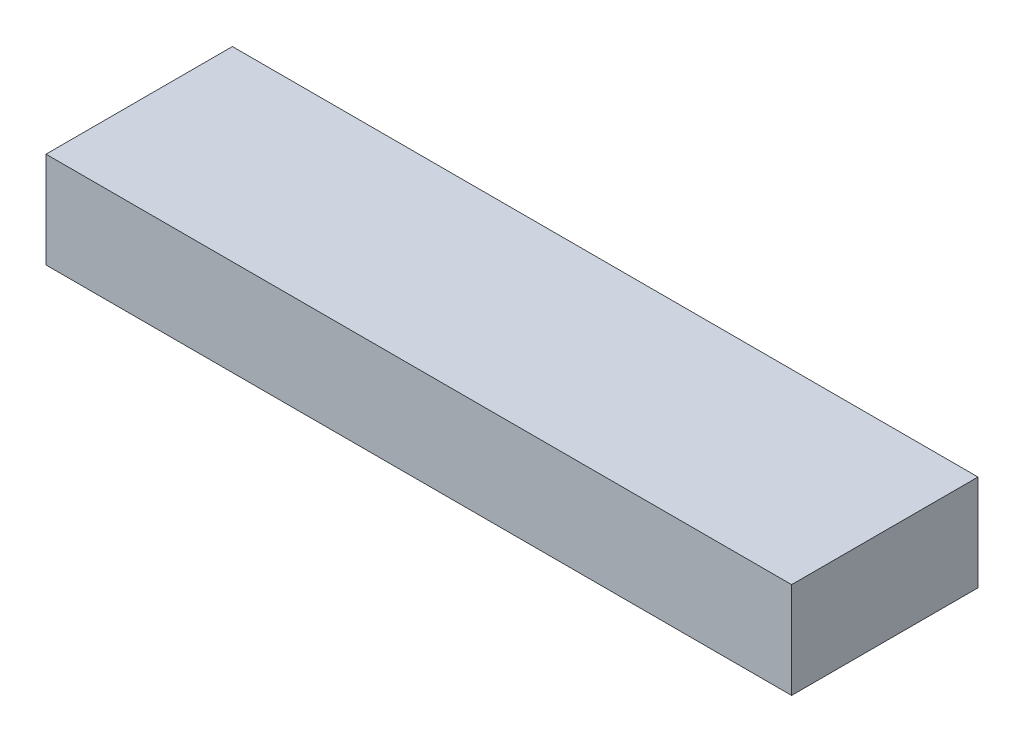
SolidWorks part; units mm, degrees
ref_plane "Front Plane" through (0, 0, 0) normal (0, 0, 1) x (1, 0, 0)
ref_plane "Top Plane" through (0, 0, 0) normal (0, 1, 0) x (1, 0, 0)
ref_plane "Right Plane" through (0, 0, 0) normal (1, 0, 0) x (0, 0, -1)
sketch "Sketch1" plane through (0, 0, 0) normal (0, 1, 0) x (1, 0, 0)
  line L1 (-8000, -2000) -> (8000, -2000)
  line L2 (-8000, -2000) -> (-8000, 2000)
  line L3 (-8000, 2000) -> (8000, 2000)
  line L4 (8000, -2000) -> (8000, 2000)
  line L5 (-8000, -2000) -> (8000, 2000) construction
  line L6 (-8000, 2000) -> (8000, -2000) construction
  point P0 (0, 0)
  dimension "D1" = 16000
  dimension "D2" = 4000
extrude "Boss-Extrude1" add sketch "Sketch1" along normal blind 2000 and the other way blind 60
